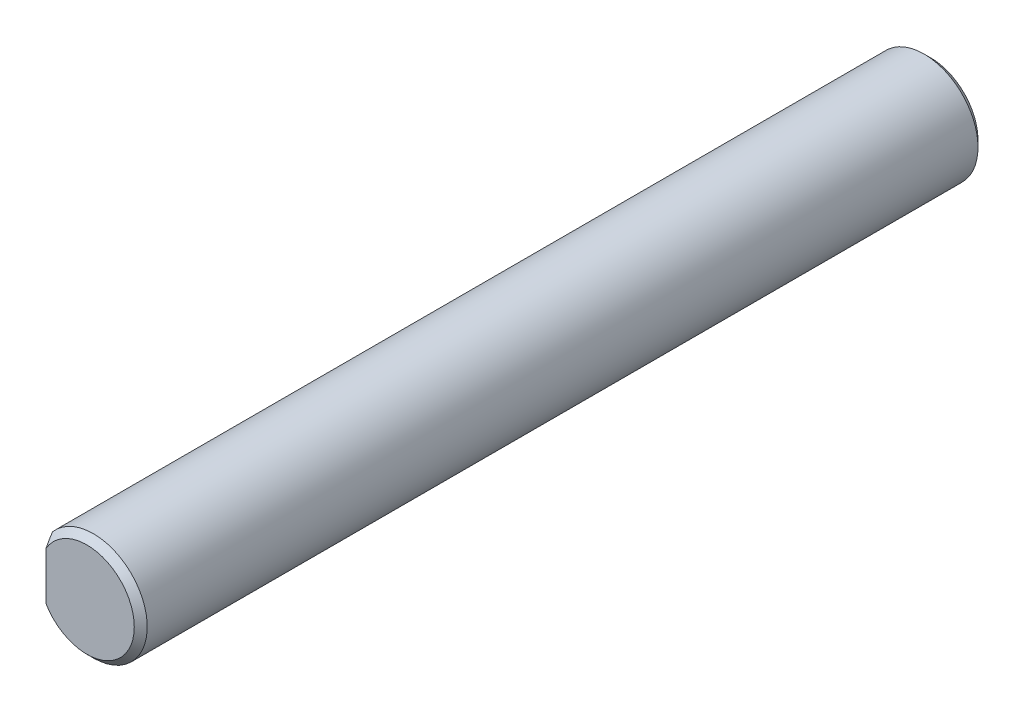
SolidWorks part; units mm, degrees
material "1023 Carbon Steel Sheet (SS)"
ref_plane "Front Plane" through (0, 0, 0) normal (0, 0, 1) x (1, 0, 0)
ref_plane "Top Plane" through (0, 0, 0) normal (0, 1, 0) x (1, 0, 0)
ref_plane "Right Plane" through (0, 0, 0) normal (1, 0, 0) x (0, 0, -1)
sketch "Sketch1" plane through (0, 0, 0) normal (0, 0, 1) x (1, 0, 0)
  circle A0 centre (0, 0) radius 4.15
  dimension "D1" = 8.3
extrude "Boss-Extrude1" add sketch "Sketch1" along normal blind 65
chamfer "Chamfer1" distance 0.5 angle 45 2 edges at (4.15, 0, 0) (4.15, 0, 65)
ref_plane "Plane1" through (0, 0, 32.5) normal (0, 0, 1) x (1, 0, 0)
sketch "Sketch2" plane through (0, 0, 32.5) normal (0, 0, 1) x (1, 0, 0)
  line L0 (0, 0) -> (-4.15, 0) construction
  line L1 (-4.4371, -3.8196) -> (-3.15, -3.8196)
  line L2 (-4.4371, -3.8196) -> (-4.4371, 3.8196)
  line L3 (-4.4371, 3.8196) -> (-3.15, 3.8196)
  line L4 (-3.15, -3.8196) -> (-3.15, 3.8196)
  circle A0 centre (0, 0) radius 4.15 construction
  point P10 (-3.15, 0)
  point P11 (-3, 3.8196)
  dimension "D1" = 1
extrude "Cut-Extrude1" cut sketch "Sketch2" against normal mid plane 66
